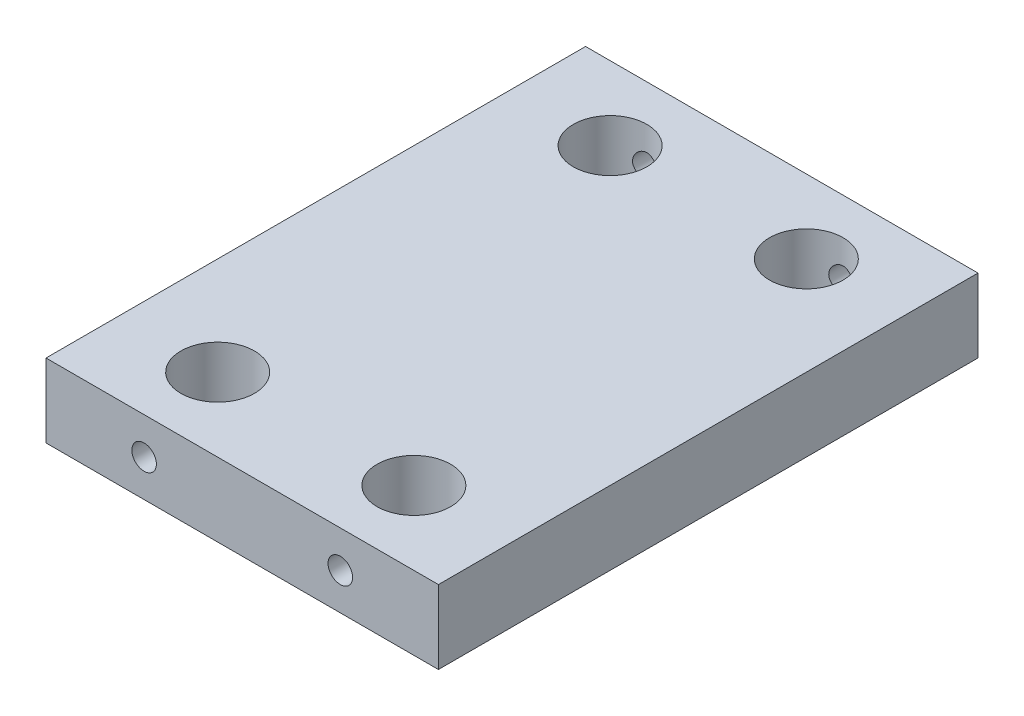
SolidWorks part; units mm, degrees
material "Pine"
ref_plane "Front Plane" through (0, 0, 0) normal (0, 0, 1) x (1, 0, 0)
ref_plane "Top Plane" through (0, 0, 0) normal (0, 1, 0) x (1, 0, 0)
ref_plane "Right Plane" through (0, 0, 0) normal (1, 0, 0) x (0, 0, -1)
sketch "Sketch1" plane through (0, 0, 0) normal (0, 1, 0) x (1, 0, 0)
  line L1 (-50.8, 69.85) -> (50.8, 69.85)
  line L2 (-50.8, 69.85) -> (-50.8, -69.85)
  line L3 (-50.8, -69.85) -> (50.8, -69.85)
  line L4 (50.8, 69.85) -> (50.8, -69.85)
  line L5 (-50.8, 69.85) -> (50.8, -69.85) construction
  line L6 (-50.8, -69.85) -> (50.8, 69.85) construction
  point P0 (0, 0)
  dimension "D1" = 139.7
  dimension "D2" = 101.6
extrude "Boss-Extrude1" add sketch "Sketch1" along normal blind 19.05
hole_wizard "3/4 (0.75) Diameter Hole1" positions "Sketch3" profile "Sketch2" hole size "3/4" standard "Ansi Inch"
sketch "Sketch3" plane through (0, 19.05, 0) normal (0, 1, 0) x (-1, 0, 0)
  line L0 (50.8, -69.85) -> (50.8, 69.85) construction
  line L1 (-50.8, -69.85) -> (50.8, -69.85) construction
  point P0 (25.4, -50.8)
  dimension "D1" = 25.4
  dimension "D2" = 19.05
sketch "Sketch2" plane through (-25.4, 19.05, -50.8) normal (1, 0, 0) x (0, 0, 1)
  line L0 (0, 0) -> (0, 24.7732)
  line L1 (0, 24.7732) -> (9.525, 19.05)
  line L2 (9.525, 19.05) -> (9.525, 0)
  line L5 (9.525, 0) -> (0, 0)
  line L10 (0, 24.7732) -> (-9.525, 19.05) construction
  line L11 (0, -6.35) -> (0, 107.95) construction
  dimension "Hole Dia." = 19.05
  dimension "Hole Depth" = 19.05
  dimension "Drill Angle" = 118
mirror "Mirror1" about plane through (0, 0, 0) normal (0, 0, 1) of "3/4 (0.75) Diameter Hole1"
mirror "Mirror4" about plane through (0, 0, 0) normal (1, 0, 0) of "Mirror1", "3/4 (0.75) Diameter Hole1"
hole_wizard "1/4 (0.25) Diameter Hole1" positions "Sketch5" profile "Sketch4" hole size "1/4" standard "Ansi Inch"
sketch "Sketch5" plane through (0, 0, -69.85) normal (0, 0, -1) x (-1, 0, 0)
  line L0 (-50.8, 19.05) -> (-50.8, 0) construction
  line L1 (-50.8, 0) -> (50.8, 0) construction
  point P0 (-25.4, 9.525)
  dimension "D1" = 25.4
  dimension "D2" = 9.525
sketch "Sketch4" plane through (25.4, 9.525, -69.85) normal (1, 0, 0) x (0, 1, 0)
  line L0 (0, 0) -> (0, 20.9577)
  line L1 (0, 20.9577) -> (3.175, 19.05)
  line L2 (3.175, 19.05) -> (3.175, 0)
  line L5 (3.175, 0) -> (0, 0)
  line L10 (0, 20.9577) -> (-3.175, 19.05) construction
  line L11 (0, -6.35) -> (0, 107.95) construction
  dimension "Hole Dia." = 6.35
  dimension "Hole Depth" = 19.05
  dimension "Drill Angle" = 118
mirror "Mirror5" about plane through (0, 0, 0) normal (0, 0, 1) of "1/4 (0.25) Diameter Hole1"
mirror "Mirror10" about plane through (0, 0, 0) normal (1, 0, 0) of "Mirror5", "1/4 (0.25) Diameter Hole1"
